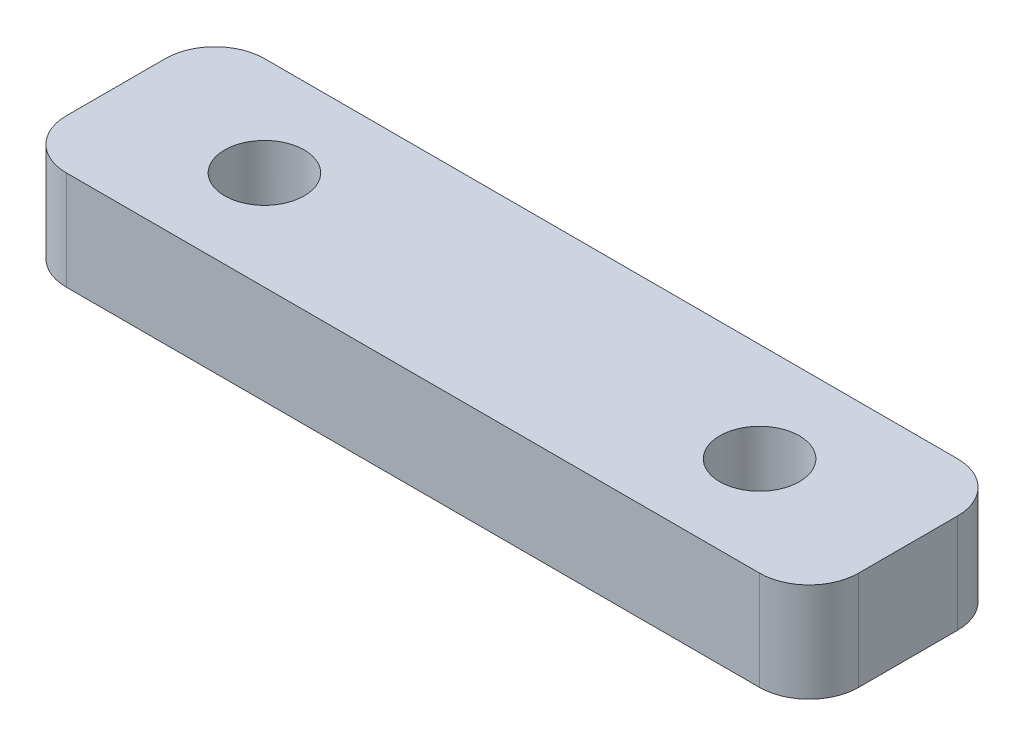
SolidWorks part; units mm, degrees
ref_plane "Front Plane" through (0, 0, 0) normal (0, 0, 1) x (1, 0, 0)
ref_plane "Top Plane" through (0, 0, 0) normal (0, 1, 0) x (1, 0, 0)
ref_plane "Right Plane" through (0, 0, 0) normal (1, 0, 0) x (0, 0, -1)
sketch "Sketch1" plane through (0, 0, 0) normal (0, 1, 0) x (1, 0, 0)
  line L0 (0, -6.35) -> (50.8, -6.35) construction
  line L1 (0, 0) -> (50.8, 0)
  line L2 (0, 0) -> (0, -12.7)
  line L3 (0, -12.7) -> (50.8, -12.7)
  line L4 (50.8, 0) -> (50.8, -12.7)
  line L5 (9.525, -12.7) -> (9.525, 3.7009) construction
  line L6 (41.275, -12.7) -> (41.275, 5.8033) construction
  dimension "D1" = 50.8
  dimension "D2" = 12.7
  dimension "D3" = 9.525
  dimension "D4" = 9.525
extrude "Boss-Extrude1" add sketch "Sketch1" along normal blind 6.35 contours L3 L4 L1 L2
hole_wizard "Tap Drill for 1/4-20 Tap1" positions "Sketch2" profile "Sketch3" hole size "1/4-20" standard "ANSI Inch" end condition up to next
sketch "Sketch2" plane through (0, 0, 0) normal (0, -1, 0) x (-1, 0, 0)
  line L0 (0, 0) -> (0, -12.7) construction
  line L1 (-50.8, 0) -> (-50.8, -12.7) construction
  line L2 (0, -12.7) -> (-50.8, -12.7) construction
  point P0 (-9.525, -6.35)
  point P2 (-41.275, -6.35)
  dimension "D1" = 9.525
  dimension "D2" = 9.525
  dimension "D3" = 6.35
  dimension "D4" = 6.35
sketch "Sketch3" plane through (9.525, 0, 6.35) normal (1, 0, 0) x (0, 0, -1)
  line L0 (0, 0) -> (0, 6.35)
  line L1 (0, 6.35) -> (2.5527, 6.35)
  line L2 (2.5527, 6.35) -> (2.5527, 0)
  line L5 (2.5527, 0) -> (0, 0)
  line L11 (0, -6.35) -> (0, 107.95) construction
  dimension "Thru Hole Dia." = 5.1054
  dimension "Thru Hole Depth" = 6.35
fillet "Fillet1" radius 3.175 4 edges at (50.8, 3.175, 0) (50.8, 3.175, 12.7) (0, 3.175, 0) (0, 3.175, 12.7)
